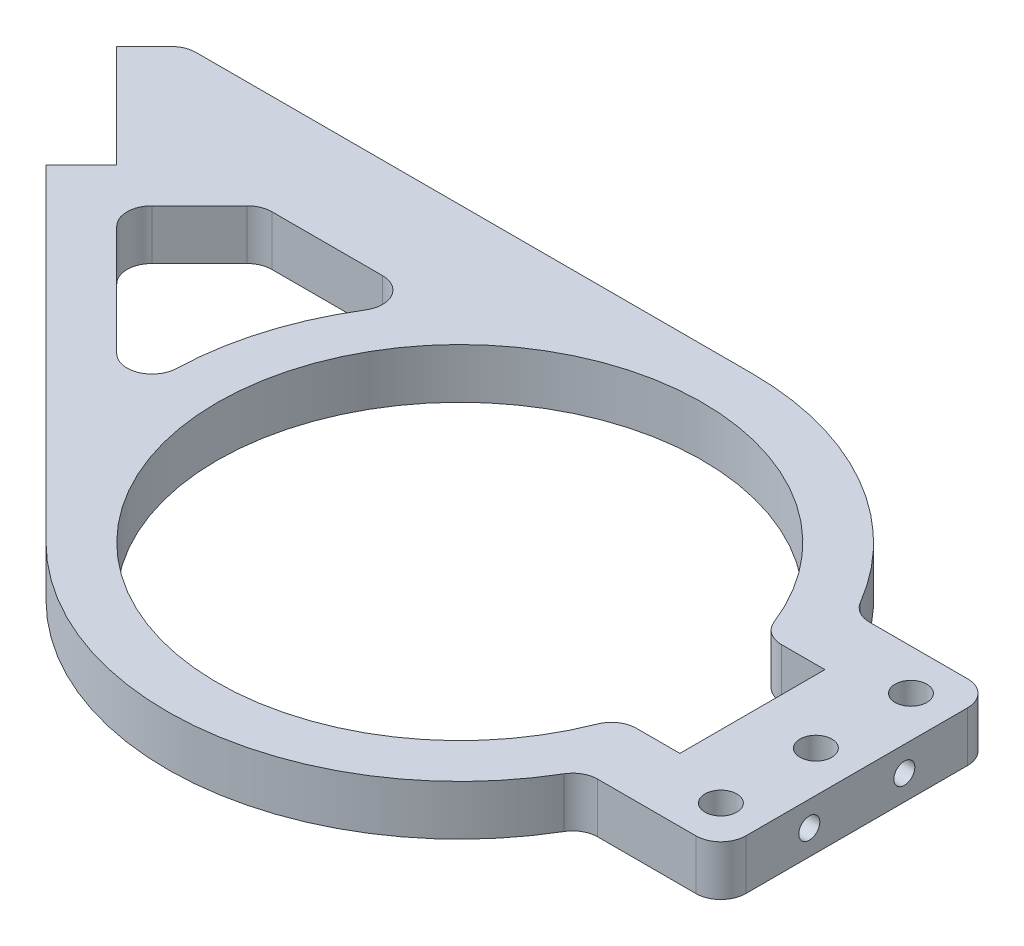
SolidWorks part; units mm, degrees
material "1060 Alloy"
ref_plane "Front Plane" through (0, 0, 0) normal (0, 0, 1) x (1, 0, 0)
ref_plane "Top Plane" through (0, 0, 0) normal (0, 1, 0) x (1, 0, 0)
ref_plane "Right Plane" through (0, 0, 0) normal (1, 0, 0) x (0, 0, -1)
sketch "Sketch1" plane through (0, 0, 0) normal (0, 1, 0) x (1, 0, 0)
  line L0 (0, 0) -> (58.5, 0) construction
  line L1 (58.5, -14.5) -> (58.5, 14.5)
  line L2 (58.5, 14.5) -> (46.2817, 14.5)
  line L3 (58.5, -14.5) -> (46.2817, -14.5)
  line L4 (48.5, 14.5) -> (48.5, -14.5) construction
  line L5 (-127.2969, 44.5654) -> (-106.7554, 24.024) construction
  line L6 (-106.7554, 24.024) -> (-175.3448, -44.5654) construction
  line L7 (-175.3448, -44.5654) -> (-195.8863, -24.024) construction
  line L8 (-195.8863, -24.024) -> (-127.2969, 44.5654) construction
  line L9 (-81.6517, -1.0798) -> (-14.4422, -68.2893) construction
  line L10 (-163.9272, -55.983) -> (-126.5132, -93.397) construction
  line L11 (-141.0501, -10.2707) -> (-161.5916, 10.2707) construction
  line L12 (-151.3209, 0) -> (0, 0) construction
  line L13 (-120.1905, 51.6011) -> (-99.6844, 31.095)
  line L14 (-99.6844, 31.095) -> (-106.7554, 24.024)
  line L15 (-106.7554, 24.024) -> (-41.3657, -41.3657)
  line L16 (-120.1905, 51.6011) -> (-113.2916, 58.5)
  line L17 (-113.2916, 58.5) -> (0, 58.5)
  line L18 (-92.6133, 24.024) -> (-57.4247, -11.1646)
  line L19 (-92.6133, 24.024) -> (-78.1373, 38.5)
  line L20 (-78.1373, 38.5) -> (-44.0454, 38.5)
  line L21 (71.2, 9.5) -> (71.2, -9.5) construction
  line L22 (71.2, 9.5) -> (71.2, 28.5) construction
  line L23 (71.2, -9.5) -> (71.2, -28.5) construction
  line L24 (51.8051, 27.175) -> (79.375, 27.175)
  line L25 (79.375, 27.175) -> (79.375, -27.175)
  line L26 (51.8051, -27.175) -> (79.375, -27.175)
  arc A0 (46.2817, 14.5) -> (46.2817, -14.5) centre (0, 0) ccw
  arc A1 (51.8051, 27.175) -> (0, 58.5) centre (0, 0) ccw
  arc A2 (46.2817, 14.5) -> (46.2817, -14.5) centre (0, 0) cw construction
  circle A3 centre (71.2, 9.5) radius 3.175 construction
  circle A4 centre (71.2, -9.5) radius 3.175 construction
  circle A7 centre (71.2, 19) radius 3.175 construction
  circle A8 centre (71.2, 0) radius 3.175 construction
  circle A9 centre (71.2, -19) radius 3.175 construction
  arc A10 (-44.0454, 38.5) -> (-57.4247, -11.1646) centre (0, 0) ccw
  arc A11 (-41.3657, -41.3657) -> (51.8051, -27.175) centre (0, 0) ccw
  point P3 (71.2, 28.5)
  point P33 (71.2, 0)
  point P48 (71.2, 19)
  point P49 (71.2, 0)
  point P52 (79.375, 0)
  point P53 (71.2, -19)
  point P54 (71.2, -28.5)
  dimension "D1" = 97
  dimension "D2" = 10
  dimension "D13" = 6.35
  dimension "D15" = 12.7
  dimension "D16" = 5
  dimension "D17" = 5
  dimension "D3" = 29
  dimension "D4" = 10
  dimension "D5" = 29.05
  dimension "D6" = 97
  dimension "D7" = 45
  dimension "D8" = 29
  dimension "D9" = 10
  dimension "D10" = 20
  dimension "D11" = 10
  dimension "D12" = 10
  dimension "D14" = 19
extrude "Boss-Extrude1" add sketch "Sketch1" against normal mid plane 10
sketch "Sketch2" plane through (58.5, 0, 0) normal (-1, 0, 0) x (0, 0, 1)
  line L0 (-14.5, 0) -> (14.5, 0) construction
  line L1 (-14.5, -5) -> (-14.5, 5) construction
  line L2 (14.5, -5) -> (14.5, 5) construction
  line L3 (0, -5) -> (0, 5) construction
  line L4 (14.5, -5) -> (-14.5, -5) construction
  line L5 (14.5, 5) -> (-14.5, 5) construction
  point P6 (-9.5, 0)
  point P14 (9.5, 0)
  dimension "D1" = 19
sketch "Sketch3" plane through (-34.2947, 0, 34.2947) normal (-0.7071, 0, 0.7071) x (0.7071, 0, 0.7071)
  line L0 (-121.475, 0) -> (-92.475, 0) construction
  line L1 (-121.475, -5) -> (-121.475, 5) construction
  line L2 (-92.475, -5) -> (-92.475, 5) construction
  line L3 (-106.975, -5) -> (-106.975, 5) construction
  line L4 (-121.475, -5) -> (-92.475, -5) construction
  line L5 (-121.475, 5) -> (-92.475, 5) construction
  point P12 (-116.475, 0)
  point P13 (-97.475, 0)
  dimension "D1" = 19
hole_wizard "M5x0.8 Tapped Hole1" positions "Sketch4" profile "Sketch6" tap size "M5x0.8" standard "ANSI Metric"
sketch "Sketch4" plane through (-34.2947, 0, 34.2947) normal (-0.7071, 0, 0.7071) x (0.7071, 0, 0.7071)
  point P0 (-116.475, 0)
  point P3 (-97.475, 0)
sketch "Sketch6" plane through (-116.6549, 0, -48.0656) normal (0, 1, 0) x (0.7071, 0, 0.7071)
  line L0 (0, 0) -> (0, 41.2618)
  line L1 (0, 41.2618) -> (2.1, 40)
  line L2 (2.1, 40) -> (2.1, 0.425)
  line L3 (2.1, 0.425) -> (2.525, 0)
  line L5 (2.525, 0) -> (0, 0)
  line L6 (-2.1, 0.425) -> (-2.525, 0) construction
  line L10 (0, 41.2618) -> (-2.1, 40) construction
  line L11 (0, -6.35) -> (0, 107.95) construction
  dimension "Tap Drill Dia." = 4.2
  dimension "Tap Drill Depth" = 40
  dimension "Near C'Sink Dia." = 5.05
  dimension "Near C'Sink Angle" = 90
  dimension "Drill Angle" = 118
cosmetic thread "Hole Thread1" parameters "D1"=30, "D2"=5
cosmetic thread "Hole Thread2" parameters "D1"=16.8315, "D2"=5
hole_wizard "M5x0.8 Tapped Hole2" positions "Sketch7" profile "Sketch8" tap size "M5x0.8" standard "ANSI Metric"
sketch "Sketch7" plane through (58.5, 0, 0) normal (-1, 0, 0) x (0, 0, 1)
  point P0 (-9.5, 0)
  point P3 (9.5, 0)
cosmetic thread "Hole Thread3" parameters "D2"=5
cosmetic thread "Hole Thread4" parameters "D2"=5
sketch "Sketch8" plane through (58.5, 0, -9.5) normal (0, 1, 0) x (0, 0, 1)
  line L0 (0, 0) -> (0, 20.875)
  line L1 (0, 20.875) -> (2.1, 20.875)
  line L2 (2.1, 20.875) -> (2.1, 0.425)
  line L3 (2.1, 0.425) -> (2.525, 0)
  line L5 (2.525, 0) -> (0, 0)
  line L6 (-2.1, 0.425) -> (-2.525, 0) construction
  line L11 (0, -6.35) -> (0, 107.95) construction
  dimension "Thru Tap Drill Dia." = 4.2
  dimension "Thru Tap Drill Depth" = 20.875
  dimension "Near C'Sink Dia." = 5.05
  dimension "Near C'Sink Angle" = 90
hole_wizard "1/4 (0.25) Diameter Hole1" positions "Sketch9" profile "Sketch10" hole size "1/4" standard "ANSI Inch" end condition through all
sketch "Sketch9" plane through (0, 5, 0) normal (0, 1, 0) x (1, 0, 0)
  point P3 (71.2, 19)
  point P6 (71.2, 0)
  point P9 (71.2, -19)
sketch "Sketch10" plane through (71.2, 5, -19) normal (1, 0, 0) x (0, 0, 1)
  line L0 (0, 0) -> (0, 10)
  line L1 (0, 10) -> (3.175, 10)
  line L2 (3.175, 10) -> (3.175, 0)
  line L5 (3.175, 0) -> (0, 0)
  line L11 (0, -6.35) -> (0, 107.95) construction
  dimension "Thru Hole Dia." = 6.35
  dimension "Thru Hole Depth" = 10
fillet "Fillet1" radius 5 11 edges at (79.375, 0, -27.175) (79.375, 0, 27.175) (51.8051, 0, 27.175) (51.8051, 0, -27.175) (-113.2916, 0, -58.5) (-92.6133, 0, -24.024) (-78.1373, 0, -38.5) (-57.4247, 0, 11.1646) (-44.0454, 0, -38.5) (46.2817, 0, 14.5) (46.2817, 0, -14.5)
